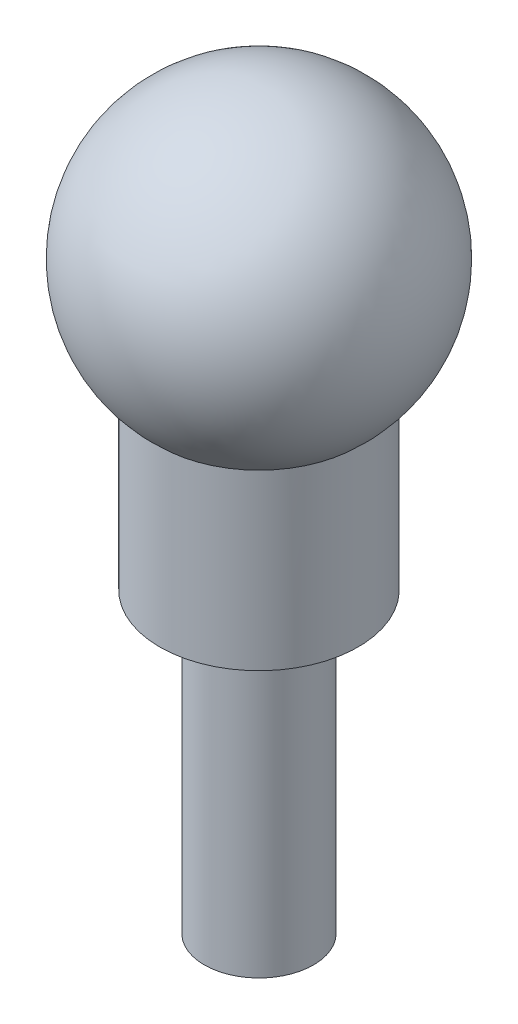
SolidWorks part; units mm, degrees
ref_plane "Front Plane" through (0, 0, 0) normal (0, 0, 1) x (1, 0, 0)
ref_plane "Top Plane" through (0, 0, 0) normal (0, 1, 0) x (1, 0, 0)
ref_plane "Right Plane" through (0, 0, 0) normal (1, 0, 0) x (0, 0, -1)
sketch "Sketch1" plane through (0, 0, 0) normal (0, 1, 0) x (1, 0, 0)
  circle A0 centre (0, 0) radius 2.2
extrude "Boss-Extrude1" add sketch "Sketch1" along normal blind 12
sketch "Sketch3" plane through (0, 12, 0) normal (0, 1, 0) x (1, 0, 0)
  circle A0 centre (0, 0) radius 4
extrude "Boss-Extrude2" add sketch "Sketch3" along normal blind 7
sketch "Sketch4" plane through (0, 0, 0) normal (0, 0, 1) x (1, 0, 0)
  line L0 (4, 19) -> (-4, 19) construction
  line L1 (0, 28.1194) -> (0, 19)
  line L2 (0, 19) -> (4, 19)
  line L3 (0, 28.1194) -> (0, 29.6252)
  arc A0 (4, 19) -> (0, 29.6252) centre (0, 23.5597) ccw
revolve "Revolve2" add sketch "Sketch4" angle 360 about L1
